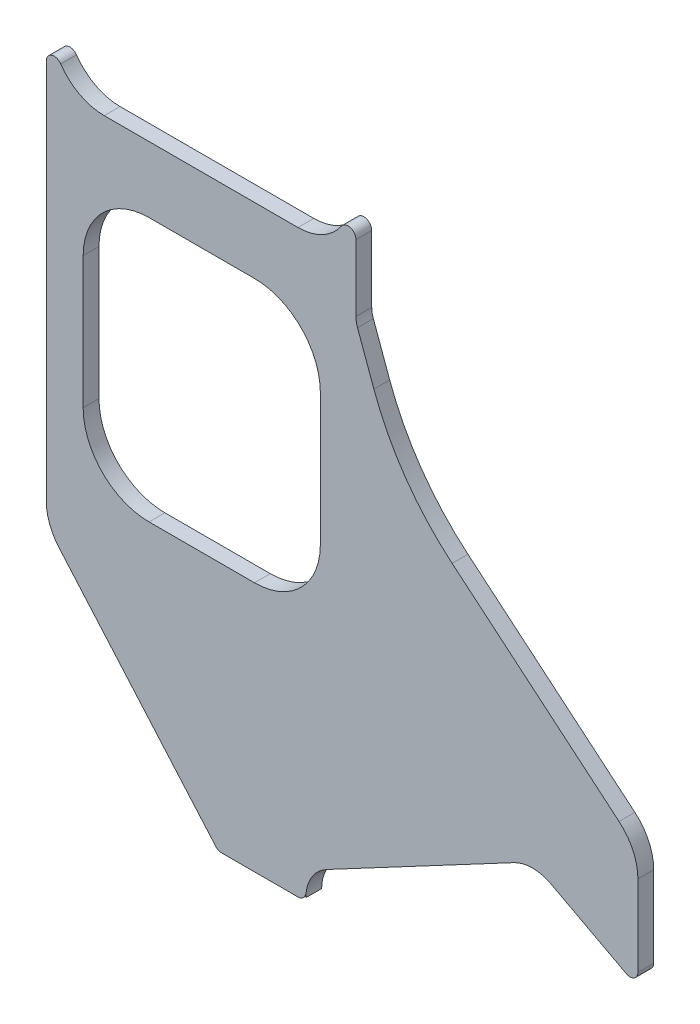
SolidWorks part; units mm, degrees
ref_plane "Plane1" through (0, 0, 0) normal (0, 0, 1) x (1, 0, 0)
ref_plane "Plane2" through (0, 0, 0) normal (0, 1, 0) x (1, 0, 0)
ref_plane "Plane3" through (0, 0, 0) normal (1, 0, 0) x (0, 0, -1)
sketch "Sketch1" plane through (0, 0, 0) normal (0, 0, 1) x (1, 0, 0)
  line L0 (-7.0421, -3.7443) -> (-78.0421, -41.4957)
  line L1 (-67, 171.0385) -> (-67, 145.7633)
  line L2 (-117.9363, -56) -> (-89, -56)
  line L3 (-86, -53) -> (-86, -54.7399)
  line L4 (-120.2004, -54.9682) -> (-179.5942, 13.3565)
  line L5 (-184.5, 26.4777) -> (-184.5, 171.0385)
  line L6 (-162.5, 164) -> (-89, 164)
  line L7 (32.8558, 29.7264) -> (-30.4997, 82.8879)
  line L8 (40, 14.4055) -> (40, -16.2755)
  line L9 (35.5916, -18.9244) -> (7.0421, -3.7443)
  line L10 (0, 0) -> (0, -28.3157) construction
  line L13 (-66.3969, 142.3431) -> (-60.1903, 125.2904)
  line L15 (-145.5, 139) -> (-105.5, 139)
  line L16 (-170.5, 114) -> (-170.5, 64)
  line L17 (-145.5, 39) -> (-105.5, 39)
  line L18 (-80.5, 114) -> (-80.5, 64)
  arc A0 (-30.4997, 82.8879) -> (-60.1903, 125.2904) centre (33.779, 159.4924) cw
  arc A1 (-7.0421, -3.7443) -> (7.0421, -3.7443) centre (0, -16.9886) cw
  arc A2 (-162.5, 164) -> (-179.0217, 172.7291) centre (-162.5, 184) cw
  arc A3 (-67, 145.7633) -> (-66.3969, 142.3431) centre (-57, 145.7633) ccw
  arc A4 (-179.5942, 13.3565) -> (-184.5, 26.4777) centre (-164.5, 26.4777) cw
  arc A5 (40, -16.2755) -> (35.5916, -18.9244) centre (37, -16.2755) cw
  arc A6 (-86, -54.7399) -> (-78.0421, -41.4957) centre (-71, -54.7399) cw
  arc A7 (-89, -56) -> (-86, -53) centre (-89, -53) ccw
  arc A8 (32.8558, 29.7264) -> (40, 14.4055) centre (20, 14.4055) cw
  arc A9 (-105.5, 139) -> (-80.5, 114) centre (-105.5, 114) cw
  arc A10 (-145.5, 139) -> (-170.5, 114) centre (-145.5, 114) ccw
  arc A11 (-170.5, 64) -> (-145.5, 39) centre (-145.5, 64) ccw
  arc A12 (-105.5, 39) -> (-80.5, 64) centre (-105.5, 64) ccw
  arc A13 (-120.2004, -54.9682) -> (-117.9363, -56) centre (-117.9363, -53) ccw
  arc A14 (-179.0217, 172.7291) -> (-184.5, 171.0385) centre (-181.5, 171.0385) ccw
  arc A15 (-89, 164) -> (-72.4783, 172.7291) centre (-89, 184) ccw
  arc A16 (-72.4783, 172.7291) -> (-67, 171.0385) centre (-70, 171.0385) cw
  point P4 (-184.5, 19)
  point P25 (-67, 144)
  point P31 (40, -21.2684)
  point P40 (40, 23.7316)
  dimension "D19" = 100
  dimension "D20" = 15
  dimension "D4" = 3
  dimension "D21" = 20
  dimension "D22" = 3
  dimension "D23" = 20
  dimension "D28" = 25
  dimension "D15" = 15
  dimension "D16" = 3
  dimension "D12" = 20
  dimension "D29" = 20
  dimension "D30" = 20
  dimension "D31" = 10
  dimension "D1" = 62
  dimension "D2" = 62
  dimension "D3" = 184.5
  dimension "D5" = 145
  dimension "D6" = 40
  dimension "D7" = 41
  dimension "D8" = 164
  dimension "D9" = 86
  dimension "D10" = 73.5
  dimension "D11" = 45
  dimension "D13" = 220
  dimension "D14" = 22
  dimension "D17" = 50
  dimension "D18" = 20
  dimension "D24" = 14
  dimension "D25" = 90
  dimension "D26" = 25
  dimension "D27" = 100
extrude "Extrude1" add sketch "Sketch1" along normal blind 6
